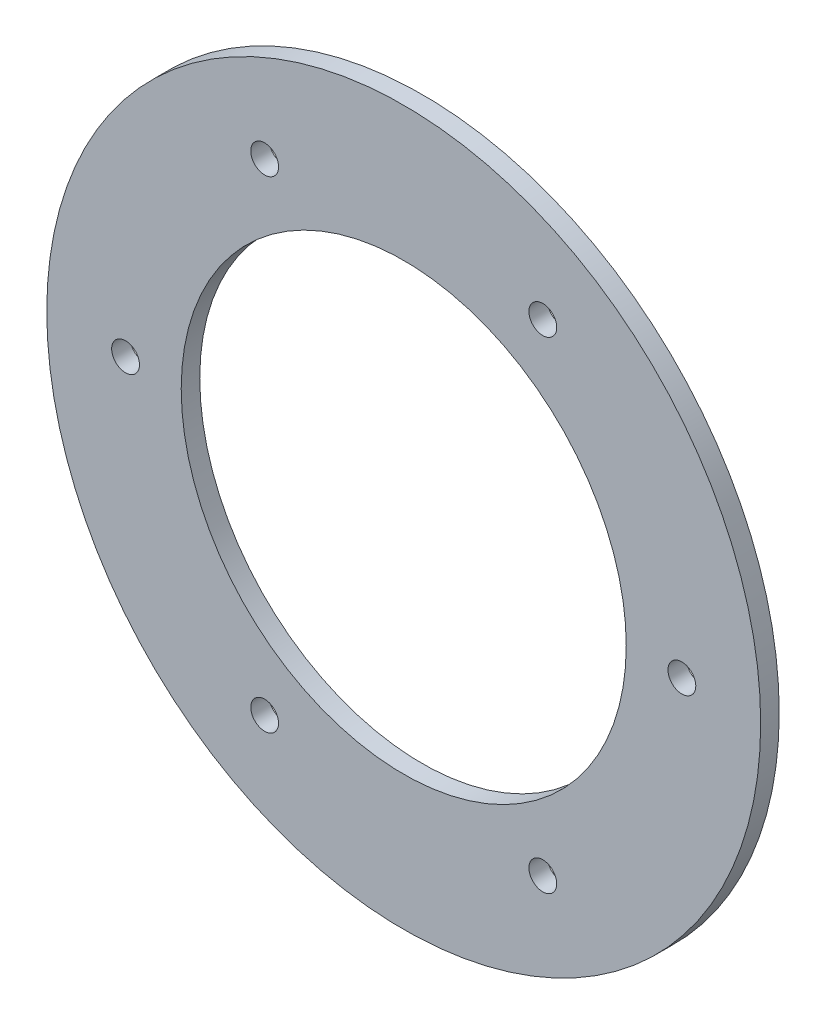
SolidWorks part; units mm, degrees
material "Acrylic (Medium-high impact)"
ref_plane "Front Plane" through (0, 0, 0) normal (0, 0, 1) x (1, 0, 0)
ref_plane "Top Plane" through (0, 0, 0) normal (0, 1, 0) x (1, 0, 0)
ref_plane "Right Plane" through (0, 0, 0) normal (1, 0, 0) x (0, 0, -1)
sketch "Model" plane through (0, 0, 0) normal (0, 0, 1) x (1, 0, 0)
  circle A340 centre (0, 0) radius 38.5
  circle A341 centre (-30, 0) radius 1.5
  circle A342 centre (-15, -25.9808) radius 1.5
  circle A343 centre (15, 25.9808) radius 1.5
  circle A344 centre (-15, 25.9808) radius 1.5
  circle A345 centre (15, -25.9808) radius 1.5
  circle A347 centre (30, 0) radius 1.5
  circle A348 centre (0, 0) radius 24
  dimension "D1" = 3
  dimension "D2" = 48
  dimension "D3" = 77
  dimension "D4" = 15
  dimension "D5" = 30
  dimension "D6" = 15
  dimension "D7" = 30
  dimension "D8" = 25.9808
  dimension "D9" = 25.9808
extrude "Boss-Extrude1" add sketch "Model" along normal blind 2
